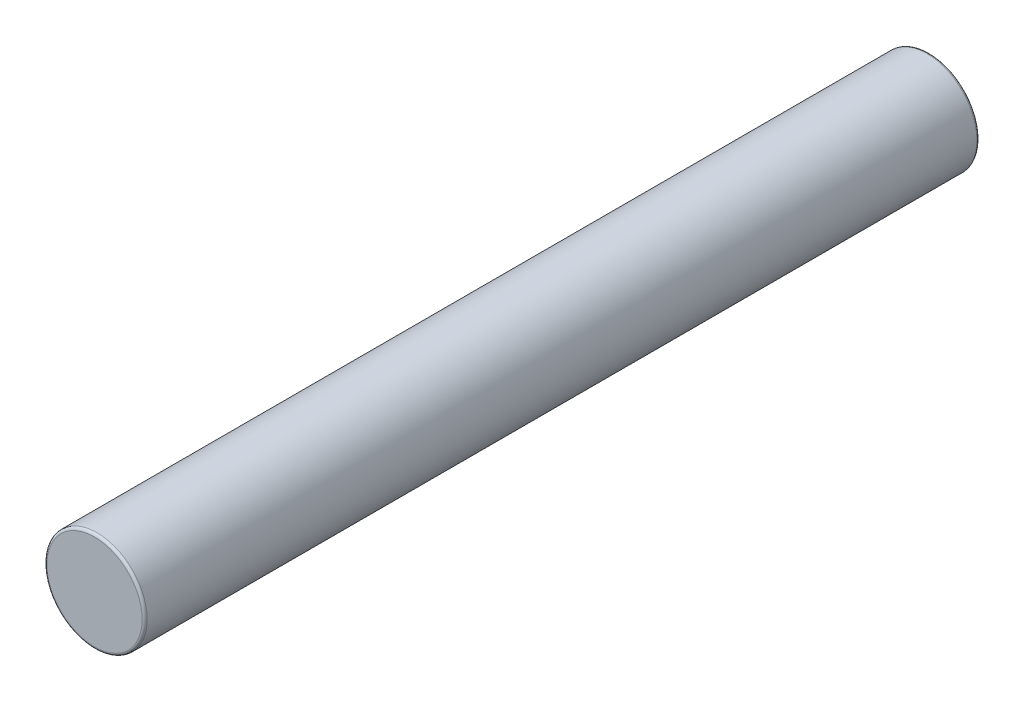
SolidWorks part; units mm, degrees
ref_plane "Front Plane" through (0, 0, 0) normal (0, 0, 1) x (1, 0, 0)
ref_plane "Top Plane" through (0, 0, 0) normal (0, 1, 0) x (1, 0, 0)
ref_plane "Right Plane" through (0, 0, 0) normal (1, 0, 0) x (0, 0, -1)
sketch "Sketch1" plane through (0, 0, 0) normal (0, 0, 1) x (1, 0, 0)
  circle A0 centre (0, 0) radius 1.5
  dimension "D1" = 3
extrude "Boss-Extrude1" add sketch "Sketch1" against normal blind 25
fillet "Fillet1" radius 0.075 2 edges at (1.5, 0, 0) (1.5, 0, -25)
